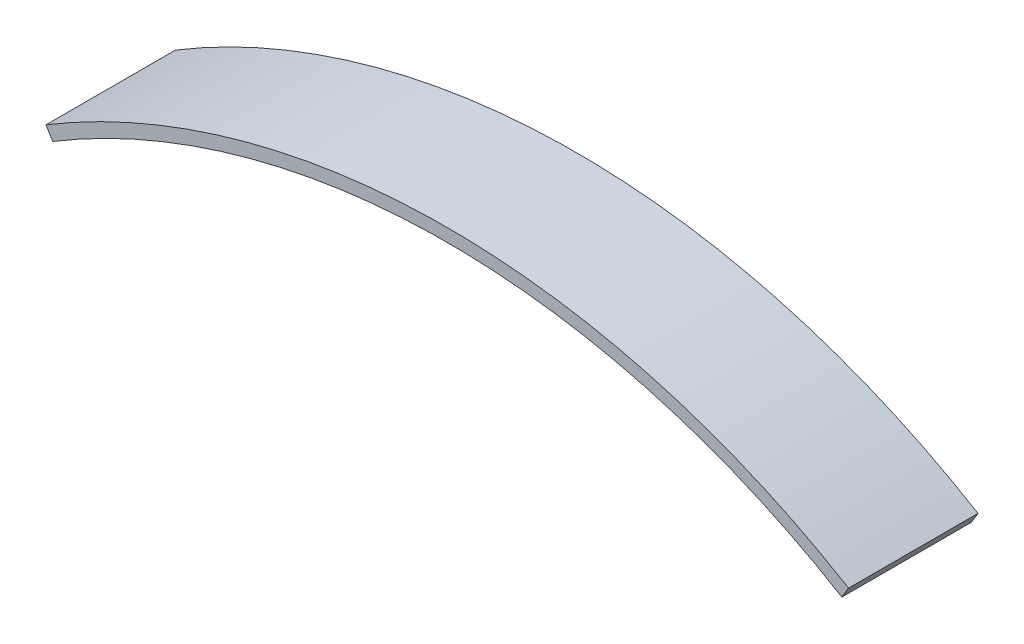
SolidWorks part; units mm, degrees
ref_plane "Front Plane" through (0, 0, 0) normal (0, 0, 1) x (1, 0, 0)
ref_plane "Top Plane" through (0, 0, 0) normal (0, 1, 0) x (1, 0, 0)
ref_plane "Right Plane" through (0, 0, 0) normal (1, 0, 0) x (0, 0, -1)
sketch "Sketch1" plane through (0, 0, 0) normal (0, 0, 1) x (1, 0, 0)
  line L0 (0, 0) -> (62, 0) construction
  line L1 (31, 0) -> (31, 11.6553) construction
  arc A0 (0, 0) -> (62, 0) centre (31, -51.3712) cw
  dimension "D2" = 60
  dimension "D1" = 62
extrude "Extrude-Thin1" add sketch "Sketch1" along normal blind 10 thin
